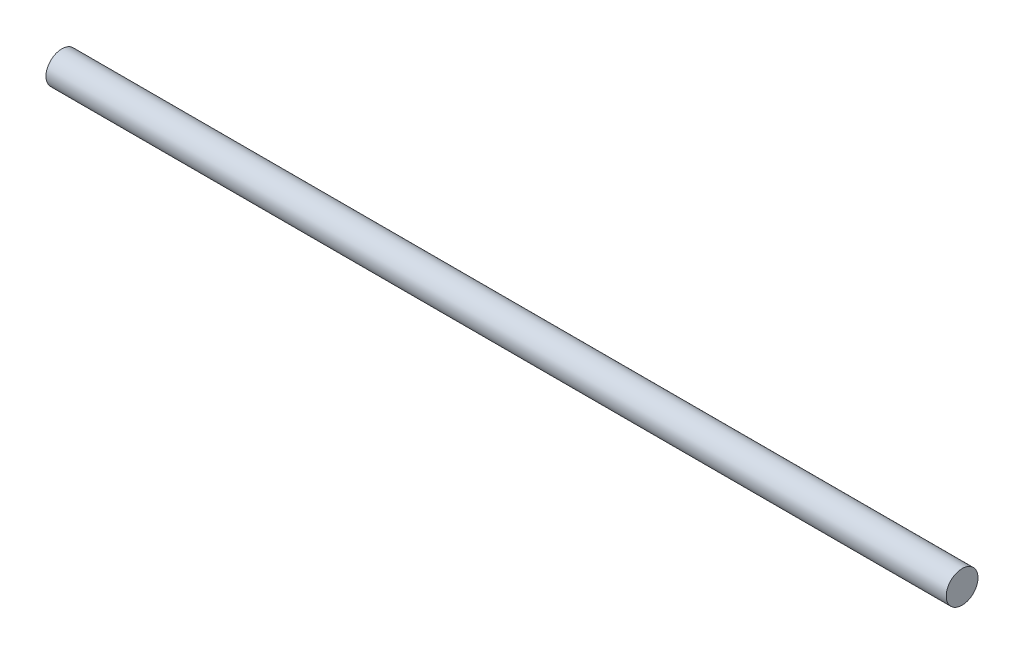
SolidWorks part; units mm, degrees
ref_plane "Front Plane" through (0, 0, 0) normal (0, 0, 1) x (1, 0, 0)
ref_plane "Top Plane" through (0, 0, 0) normal (0, 1, 0) x (1, 0, 0)
ref_plane "Right Plane" through (0, 0, 0) normal (1, 0, 0) x (0, 0, -1)
sketch "Sketch1" plane through (0, 0, 0) normal (1, 0, 0) x (0, 0, -1)
  circle A0 centre (0, 0) radius 1.5
  dimension "D1" = 3
extrude "Boss-Extrude1" add sketch "Sketch1" along normal blind 85
